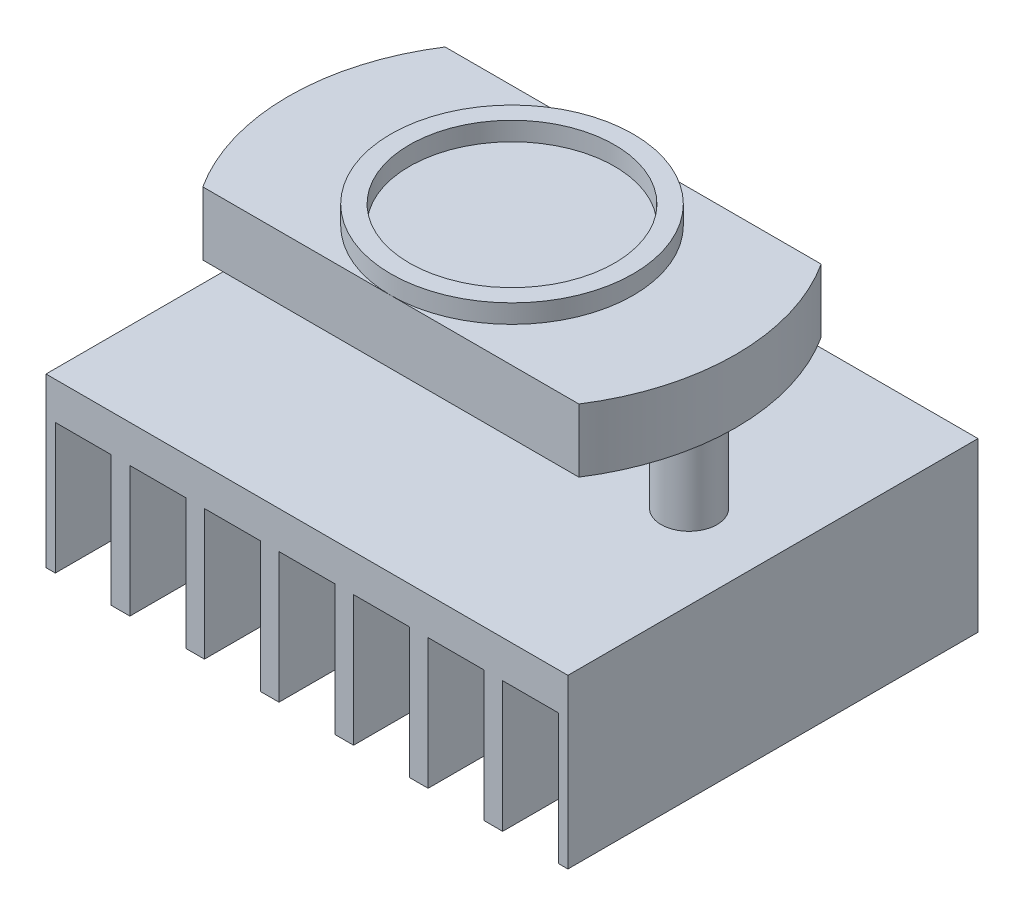
SolidWorks part; units mm, degrees
ref_plane "Piano frontale" through (0, 0, 0) normal (0, 0, 1) x (1, 0, 0)
ref_plane "Piano superiore" through (0, 0, 0) normal (0, 1, 0) x (1, 0, 0)
ref_plane "Piano destro" through (0, 0, 0) normal (1, 0, 0) x (0, 0, -1)
sketch "Schizzo1" plane through (0, 0, 0) normal (0, 1, 0) x (1, 0, 0)
  line L1 (14, -11) -> (-14, -11)
  line L2 (14, -11) -> (14, 11)
  line L3 (14, 11) -> (-14, 11)
  line L4 (-14, -11) -> (-14, 11)
  line L5 (14, -11) -> (-14, 11) construction
  line L6 (14, 11) -> (-14, -11) construction
  point P0 (0, 0)
  dimension "D1" = 22
  dimension "D2" = 28
extrude "Estrusione-Estrusione1" add sketch "Schizzo1" along normal blind 9
sketch "Schizzo2" plane through (0, 9, 0) normal (0, 1, 0) x (1, 0, 0)
  line L1 (12, 6.5) -> (-12, 6.5)
  line L2 (12, 6.5) -> (12, -6.5)
  line L3 (12, -6.5) -> (-12, -6.5)
  line L4 (-12, 6.5) -> (-12, -6.5)
  line L5 (12, 6.5) -> (-12, -6.5) construction
  line L6 (12, -6.5) -> (-12, 6.5) construction
  point P0 (0, 0)
  dimension "D1" = 13
  dimension "D2" = 24
extrude "Estrusione-Estrusione2" add sketch "Schizzo2" along normal blind 8.4
sketch "Schizzo3" plane through (0, 17.4, 0) normal (0, 1, 0) x (1, 0, 0)
  circle A0 centre (0, 0) radius 6.5
  circle A1 centre (0, 0) radius 5.5
  dimension "D1" = 11
extrude "Estrusione-Estrusione3" add sketch "Schizzo3" along normal blind 1
sketch "Schizzo5" plane through (0, 17.4, 0) normal (0, 1, 0) x (1, 0, 0)
  circle A0 centre (0, 0) radius 12
extrude "Taglio-Estrusione1" cut sketch "Schizzo5" against normal blind 10 flip side to cut
sketch "Schizzo6" plane through (0, 0, 0) normal (0, -1, 0) x (1, 0, 0)
  line L1 (14, 11) -> (-14, 11)
  line L2 (14, 11) -> (14, -11)
  line L3 (14, -11) -> (-14, -11)
  line L4 (-14, 11) -> (-14, -11)
extrude "Taglio-Estrusione2" cut sketch "Schizzo6" against normal blind 14
sketch "Schizzo7" plane through (0, 14, 0) normal (0, -1, 0) x (1, 0, 0)
  line L0 (-12, 0) -> (12, 0) construction
  arc A0 (-10.0871, 6.5) -> (-10.0871, -6.5) centre (0, 0) ccw construction
  arc A1 (10.0871, -6.5) -> (10.0871, 6.5) centre (0, 0) ccw construction
  circle A2 centre (-9.5, 0) radius 1.5
  circle A3 centre (9.5, 0) radius 1.5
  dimension "D1" = 3
  dimension "D3" = 3
  dimension "D2" = 2.5
  dimension "D4" = 2.5
extrude "Estrusione-Estrusione4" add sketch "Schizzo7" along normal blind 5
sketch3d "Schizzo3D1"
  line L0 (-8, 9, 0) -> (8, 9, 0) construction
  line L3 (14, 9, 11) -> (-14, 9, 11)
  line L4 (14, 9, 11) -> (14, 9, -11)
  line L5 (14, 9, -11) -> (-14, 9, -11)
  line L6 (-14, 9, 11) -> (-14, 9, -11)
  line L7 (14, 9, 11) -> (-14, 9, -11) construction
  line L8 (14, 9, -11) -> (-14, 9, 11) construction
  circle A1 centre (-9.5, 9, 0) radius 1.5 construction
  circle A2 centre (9.5, 9, 0) radius 1.5 construction
  point P4 (-9.5, 7.5, 0)
  point P7 (9.5, 7.5, 0)
  point P8 (0, 9, 0)
  dimension "D1" = 28
  dimension "D2" = 22
extrude "Estrusione-Estrusione5" add sketch "Schizzo3D1" along direction (0, -1, 0) on the side of the normal blind 9
sketch3d "Schizzo3D2"
  line L0 (14, 0, 11) -> (-14, 0, 11) construction
  line L1 (-13.5, 0, 11) -> (-10.5, 0, 11)
  line L2 (-13.5, 0, 11) -> (-13.5, 0, -11)
  line L3 (-13.5, 0, -11) -> (-10.5, 0, -11)
  line L4 (-10.5, 0, 11) -> (-10.5, 0, -11)
  line L5 (-14, 0, -11) -> (14, 0, -11) construction
  line L6 (-14, 0, 11) -> (-14, 0, -11) construction
  dimension "D1" = 0.5
  dimension "D2" = 3
extrude "Taglio-Estrusione3" cut sketch "Schizzo3D2" along direction (0, -1, 0) on the side against the normal blind 7
pattern_linear "Ripetizione a L1" count 7 spacing 4 along (1, 0, 0) of "Taglio-Estrusione3"
